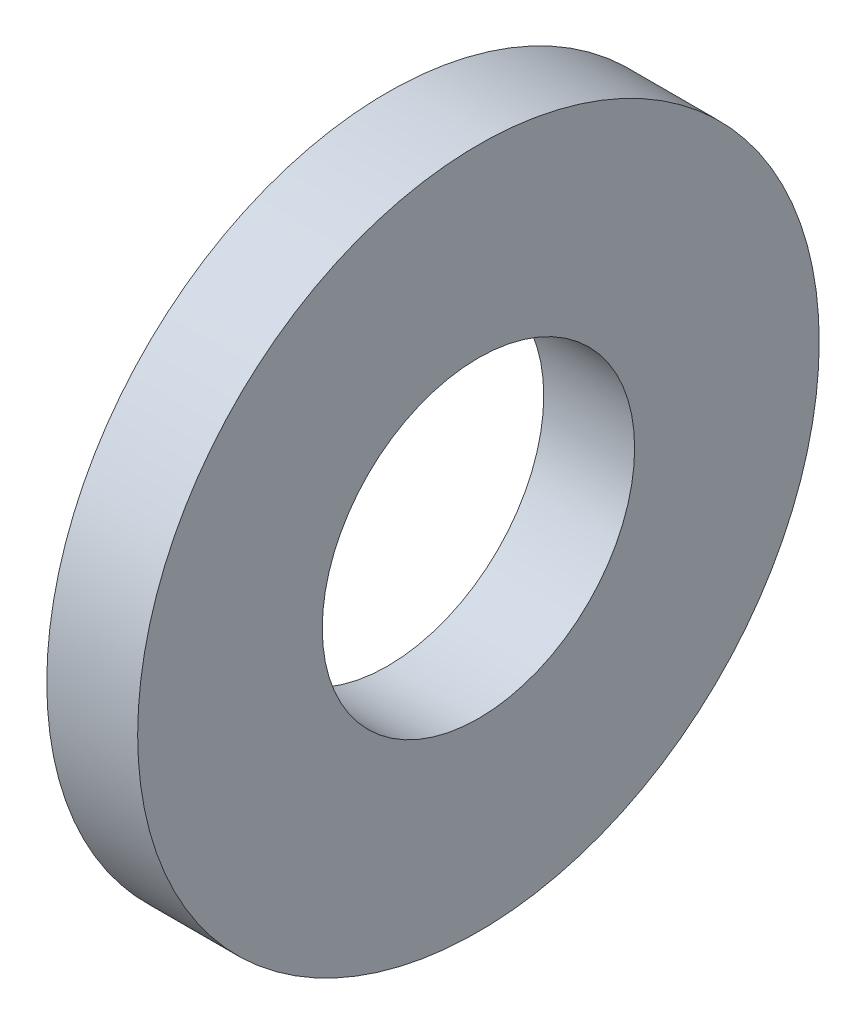
SolidWorks part; units mm, degrees
ref_plane "Plane1" through (0, 0, 0) normal (0, 0, 1) x (1, 0, 0)
ref_plane "Plane2" through (0, 0, 0) normal (0, 1, 0) x (1, 0, 0)
ref_plane "Plane3" through (0, 0, 0) normal (1, 0, 0) x (0, 0, -1)
sketch "Sketch1" plane through (0, 0, 0) normal (1, 0, 0) x (0, 0, -1)
  circle A0 centre (0, 0) radius 2.75
  circle A1 centre (0, 0) radius 6
  dimension "Insid_dia" = 5.5
  dimension "OutsideDia" = 12
extrude "Base-Extrude" add sketch "Sketch1" along normal blind 1.6
